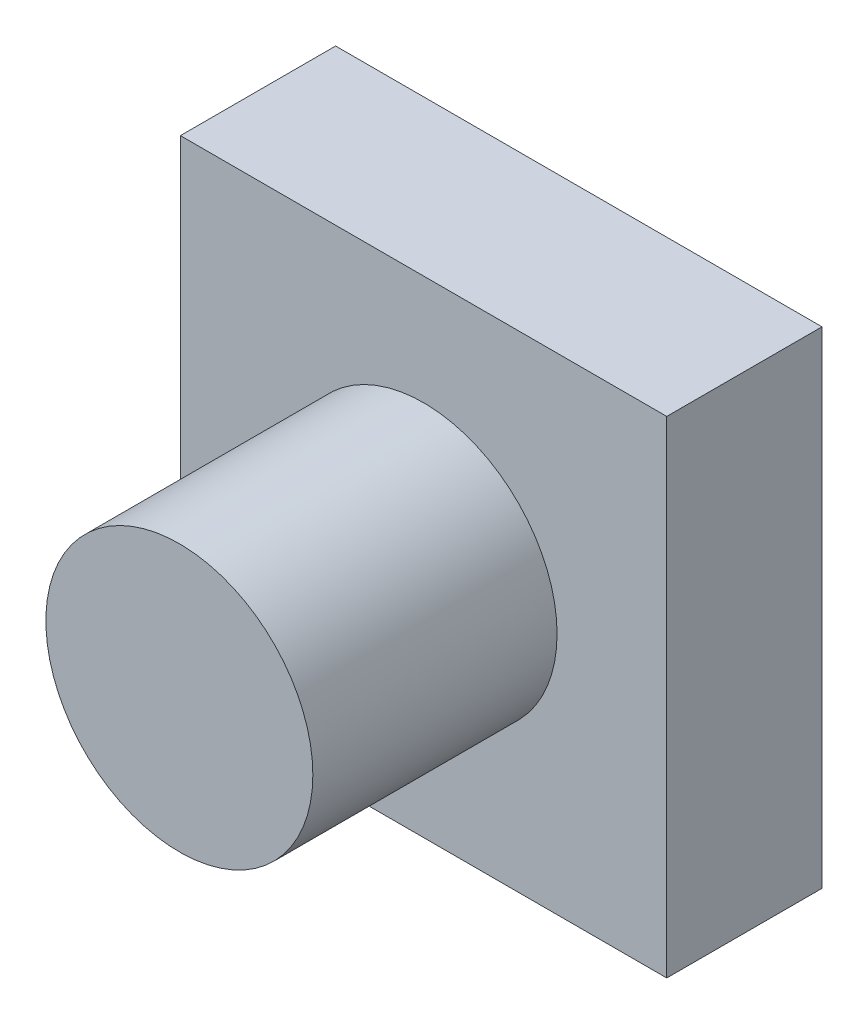
SolidWorks part; units mm, degrees
ref_plane "Front Plane" through (0, 0, 0) normal (0, 0, 1) x (1, 0, 0)
ref_plane "Top Plane" through (0, 0, 0) normal (0, 1, 0) x (1, 0, 0)
ref_plane "Right Plane" through (0, 0, 0) normal (1, 0, 0) x (0, 0, -1)
sketch "Sketch1" plane through (0, 0, 0) normal (0, 0, 1) x (1, 0, 0)
  line L1 (0, 0) -> (11.938, 0)
  line L2 (0, 0) -> (0, 11.938)
  line L3 (0, 11.938) -> (11.938, 11.938)
  line L4 (11.938, 0) -> (11.938, 11.938)
  dimension "D1" = 11.938
  dimension "D2" = 11.938
extrude "Boss-Extrude1" add sketch "Sketch1" along normal blind 3.81
sketch "Sketch2" plane through (0, 0, 3.81) normal (0, 0, 1) x (1, 0, 0)
  circle A0 centre (5.969, 5.969) radius 3.2766
  dimension "D1" = 6.5532
extrude "Boss-Extrude2" add sketch "Sketch2" along normal blind 5.9944
